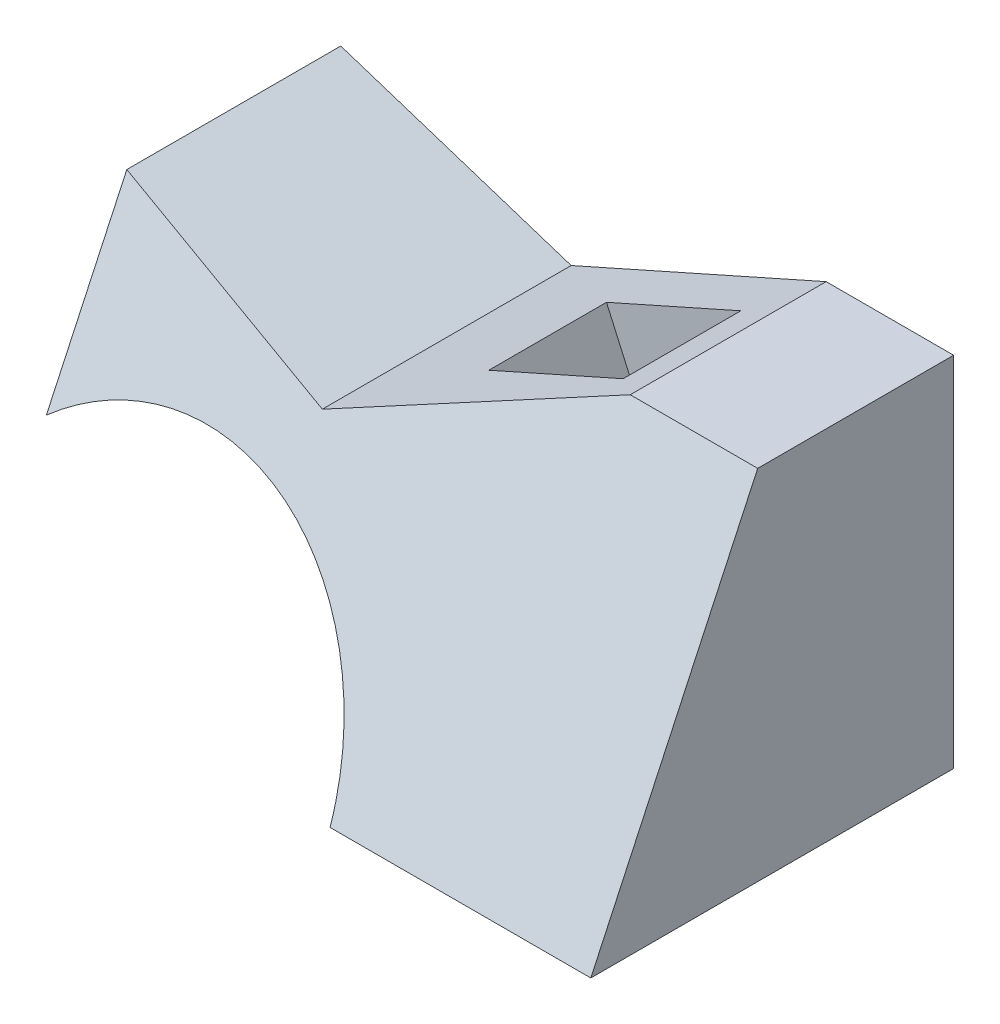
SolidWorks part; units mm, degrees
ref_plane "Front Plane" through (0, 0, 0) normal (0, 0, 1) x (1, 0, 0)
ref_plane "Top Plane" through (0, 0, 0) normal (0, 1, 0) x (1, 0, 0)
ref_plane "Right Plane" through (0, 0, 0) normal (1, 0, 0) x (0, 0, -1)
sketch "Sketch1" plane through (0, 0, 0) normal (0, 0, 1) x (1, 0, 0)
  line L1 (0, 0) -> (-53.1822, 0)
  line L2 (0, 0) -> (0, 73)
  line L3 (0, 73) -> (-26, 73)
  line L4 (-125, 29.9411) -> (-125, 65.1193)
  line L7 (-125, 65.1193) -> (-78, 49.8481)
  line L8 (-78, 49.8481) -> (-26, 73)
  arc A0 (-53.1822, 0) -> (-125, 29.9411) centre (-97, -4) ccw
  dimension "D3" = 97
  dimension "D4" = 44
  dimension "D5" = 4
  dimension "D1" = 125
  dimension "D2" = 73
  dimension "D8" = 72
  dimension "D9" = 138
  dimension "D10" = 47
  dimension "D11" = 52
extrude "Boss-Extrude1" add sketch "Sketch1" along normal blind 74
sketch "Sketch2" plane through (0, 0, 0) normal (1, 0, 0) x (0, 0, -1)
  line L0 (-74, 0) -> (-39.9595, 73)
  line L1 (-74, 73) -> (0, 73) construction
  line L2 (-74, 0) -> (0, 0) construction
  line L3 (-39.9595, 73) -> (-74, 73)
  line L4 (-74, 73) -> (-74, 0)
  dimension "D1" = 65
extrude "Cut-Extrude1" cut sketch "Sketch2" against normal through all
sketch "Sketch3" plane through (-31.4261, 70.5841, 0) normal (-0.4067, 0.9135, 0) x (0.9135, 0.4067, 0)
  line L0 (5.9396, 0) -> (5.9396, -23) construction
  line L1 (5.9396, -39.9595) -> (5.9396, 0) construction
  line L2 (5.9396, -23) -> (-16.0604, -23) construction
  line L4 (-1.0604, -35) -> (-31.0604, -35)
  line L5 (-1.0604, -35) -> (-1.0604, -11)
  line L6 (-1.0604, -11) -> (-31.0604, -11)
  line L7 (-31.0604, -35) -> (-31.0604, -11)
  line L8 (-1.0604, -35) -> (-31.0604, -11) construction
  line L9 (-1.0604, -11) -> (-31.0604, -35) construction
  dimension "D1" = 23
  dimension "D2" = 22
  dimension "D3" = 30
  dimension "D4" = 24
extrude "Cut-Extrude2" cut sketch "Sketch3" against normal blind 48
